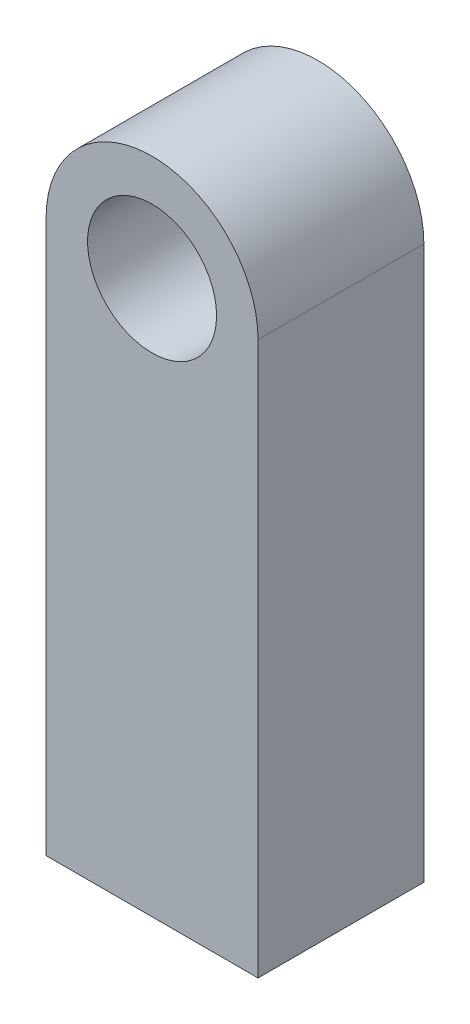
SolidWorks part; units mm, degrees
ref_plane "Alzado" through (0, 0, 0) normal (0, 0, 1) x (1, 0, 0)
ref_plane "Planta" through (0, 0, 0) normal (0, 1, 0) x (1, 0, 0)
ref_plane "Vista lateral" through (0, 0, 0) normal (1, 0, 0) x (0, 0, -1)
sketch "Croquis1" plane through (0, 0, 0) normal (0, 0, 1) x (1, 0, 0)
  line L2 (-2.875, 7.5) -> (-2.875, -7.5)
  line L3 (-2.875, -7.5) -> (2.875, -7.5)
  line L4 (2.875, 7.5) -> (2.875, -7.5)
  line L5 (-2.875, 7.5) -> (2.875, -7.5) construction
  line L6 (-2.875, -7.5) -> (2.875, 7.5) construction
  arc A0 (-2.875, 7.5) -> (2.875, 7.5) centre (0, 7.5) cw
  circle A2 centre (0, 7.5) radius 1.75
  point P0 (0, 0)
  point P9 (0, 5.75)
  point P10 (0, 0)
  point P11 (0, 0)
  point P12 (0, 7.3901)
  dimension "D3" = 3.5
  dimension "D1" = 15
  dimension "D2" = 5.75
extrude "Saliente-Extruir1" add sketch "Croquis1" along normal blind 4.5
